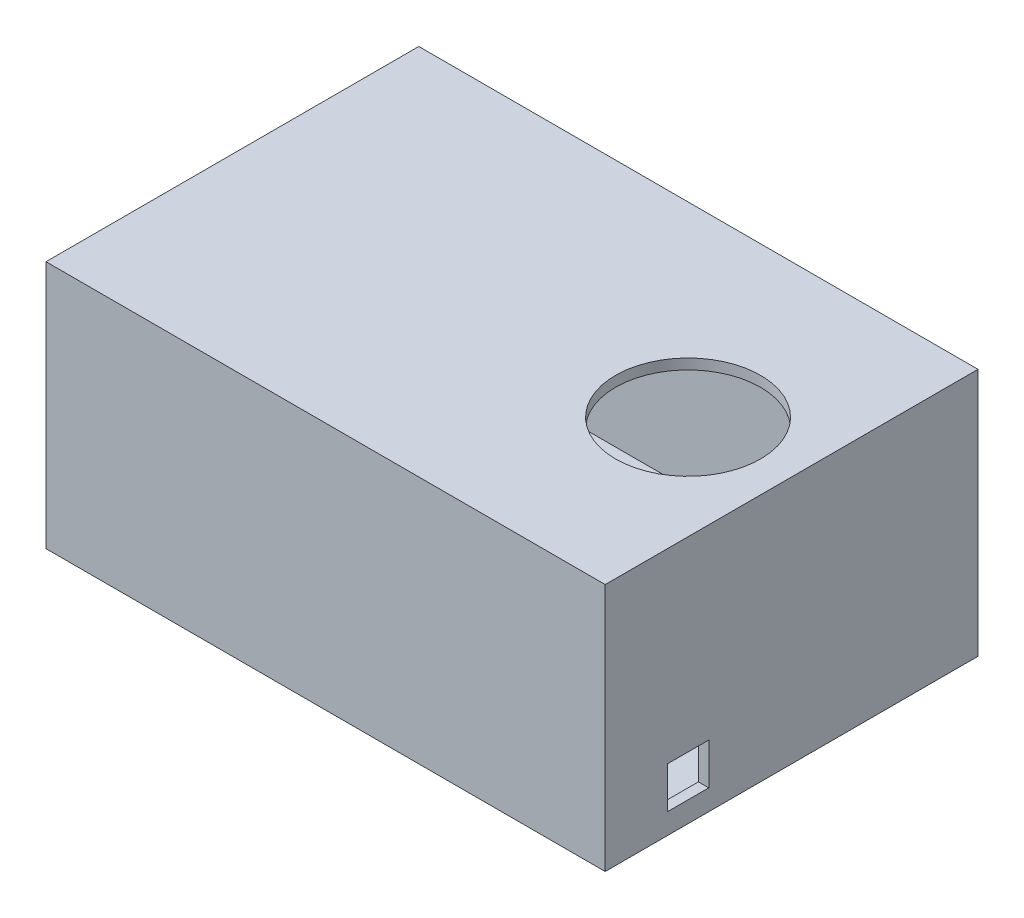
SolidWorks part; units mm, degrees
ref_plane "Front Plane" through (0, 0, 0) normal (0, 0, 1) x (1, 0, 0)
ref_plane "Top Plane" through (0, 0, 0) normal (0, 1, 0) x (1, 0, 0)
ref_plane "Right Plane" through (0, 0, 0) normal (1, 0, 0) x (0, 0, -1)
sketch "Sketch1" plane through (0, 0, 0) normal (0, 1, 0) x (1, 0, 0)
  line L1 (0, 0) -> (342.9, 0)
  line L2 (0, 0) -> (0, 228.6)
  line L3 (0, 228.6) -> (342.9, 228.6)
  line L4 (342.9, 0) -> (342.9, 228.6)
  dimension "D1" = 342.9
  dimension "D2" = 228.6
extrude "main box" add sketch "Sketch1" along normal blind 152.4
shell "Shell1" thickness 6.35
sketch "Sketch2" plane through (0, 152.4, 0) normal (0, 1, 0) x (1, 0, 0)
  line L0 (342.9, 0) -> (342.9, 228.6) construction
  circle A0 centre (279.4, 114.3) radius 44.45
  point P2 (342.9, 114.3)
  dimension "D1" = 88.9
  dimension "D2" = 63.5
extrude "top hole" cut sketch "Sketch2" against normal up to next
sketch "Sketch3" plane through (0, 0, 0) normal (-1, 0, 0) x (0, 0, 1)
  line L0 (-228.6, 0) -> (0, 0) construction
  circle A0 centre (-114.3, 76.2) radius 44.45
  point P0 (-114.3, 0)
  dimension "D1" = 88.9
  dimension "D2" = 76.2
extrude "side hole" cut sketch "Sketch3" against normal up to next
sketch "Sketch4" plane through (342.9, 0, 0) normal (1, 0, 0) x (0, 0, -1)
  line L0 (0, 0) -> (228.6, 0) construction
  line L1 (38.1, 12.7) -> (63.5, 12.7)
  line L2 (38.1, 12.7) -> (38.1, 38.1)
  line L3 (38.1, 38.1) -> (63.5, 38.1)
  line L4 (63.5, 12.7) -> (63.5, 38.1)
  line L5 (0, 152.4) -> (0, 0) construction
  dimension "D1" = 25.4
  dimension "D2" = 25.4
  dimension "D3" = 12.7
  dimension "D4" = 38.1
extrude "power cord hole" cut sketch "Sketch4" against normal up to next
